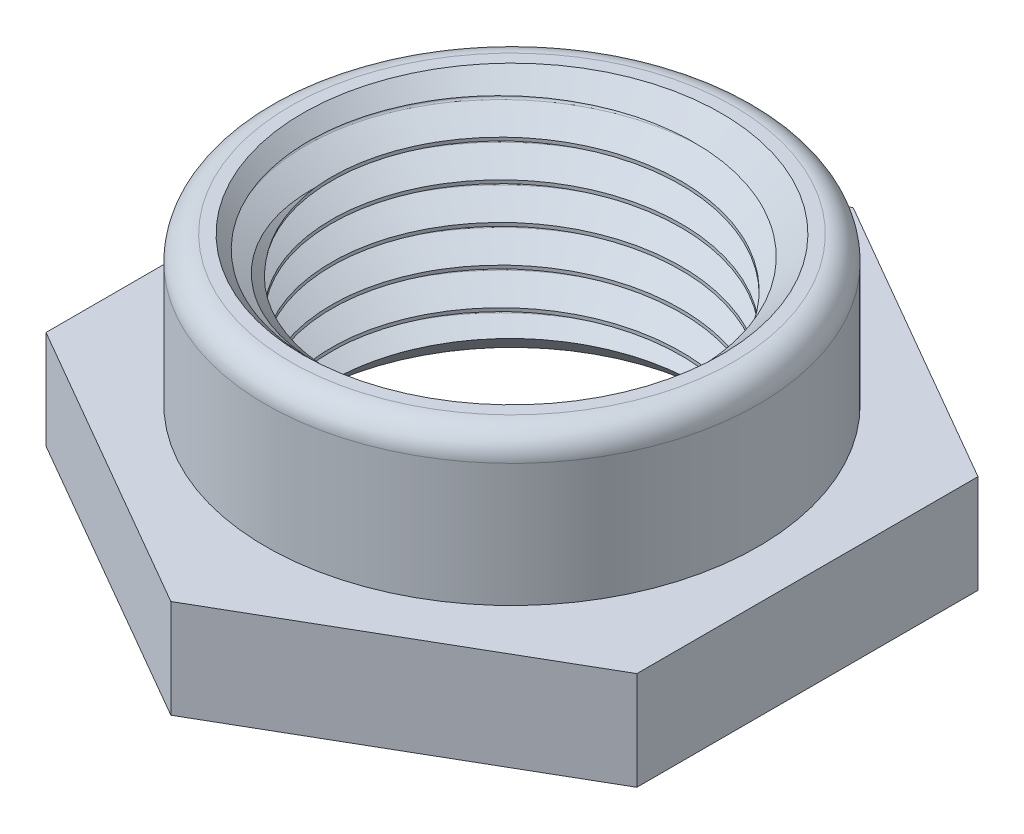
SolidWorks part; units mm, degrees
ref_plane "Спереди" through (0, 0, 0) normal (0, 0, 1) x (1, 0, 0)
ref_plane "Сверху" through (0, 0, 0) normal (0, 1, 0) x (1, 0, 0)
ref_plane "Справа" through (0, 0, 0) normal (1, 0, 0) x (0, 0, -1)
sketch "Эскиз1" plane through (0, 0, 0) normal (0, 0, 1) x (1, 0, 0)
  line L0 (0, 0) -> (3.55, 0) construction
  line L1 (0, 0) -> (0, 5) construction
  line L2 (3.55, 0) -> (3.55, 5)
  line L3 (3.55, 5) -> (4.5, 5)
  line L4 (5, 4.5) -> (5, 2)
  line L5 (5, 2) -> (7, 2)
  line L6 (7, 2) -> (7, 0)
  line L7 (7, 0) -> (3.55, 0)
  arc A0 (4.5, 5) -> (5, 4.5) centre (4.5, 4.5) cw
  dimension "D6" = 0.5
  dimension "D1" = 5
  dimension "D2" = 3.55
  dimension "D3" = 2
  dimension "D4" = 5
  dimension "D5" = 7
revolve "Повернуть1" add sketch "Эскиз1" angle 360 about L1
sketch "Эскиз4" plane through (0, 0, 0) normal (0, 0, 1) x (1, 0, 0)
  line L0 (0, 5.2609) -> (0, 0) construction
  line L1 (3.5, 5.37) -> (3.5, 4.63)
  line L2 (3.5, 5.37) -> (4.0659, 5.0433)
  line L3 (4.0659, 4.9567) -> (3.5, 4.63)
  line L4 (4.1409, 5) -> (3.5, 5) construction
  line L5 (4.5, 5) -> (-4.5, 5) construction
  arc A0 (4.0659, 4.9567) -> (4.0659, 5.0433) centre (4.0409, 5) ccw
  dimension "D4" = 0.05
  dimension "D1" = 3.5
  dimension "D2" = 0.74
  dimension "D3" = 30
  dimension "D5" = 0
sketch "Эскиз5" plane through (0, 5, 0) normal (0, 1, 0) x (1, 0, 0)
  circle A0 centre (0, 0) radius 3.5
  dimension "D1" = 7
curve "Спираль1" pitch 0.75 height 6 turns 8
chamfer "Фаска1" distance 0.7 angle 45 2 edges at (0, 5, -3.55) (0, 0, -3.55)
sweep "Вырез-По траектории9" cut profiles "Эскиз4" path "Спираль1"
sketch "Эскиз6" plane through (0, 0, 0) normal (0, -1, 0) x (1, 0, 0)
  line L1 (0, 6.9282) -> (-6, 3.4641)
  line L2 (-6, 3.4641) -> (-6, -3.4641)
  line L3 (-6, -3.4641) -> (0, -6.9282)
  line L4 (0, -6.9282) -> (6, -3.4641)
  line L5 (6, -3.4641) -> (6, 3.4641)
  line L6 (6, 3.4641) -> (0, 6.9282)
  circle A0 centre (0, 0) radius 6 construction
  circle A1 centre (0, 0) radius 7.5
extrude "Вырез-Вытянуть1" cut sketch "Эскиз6" against normal blind 10
